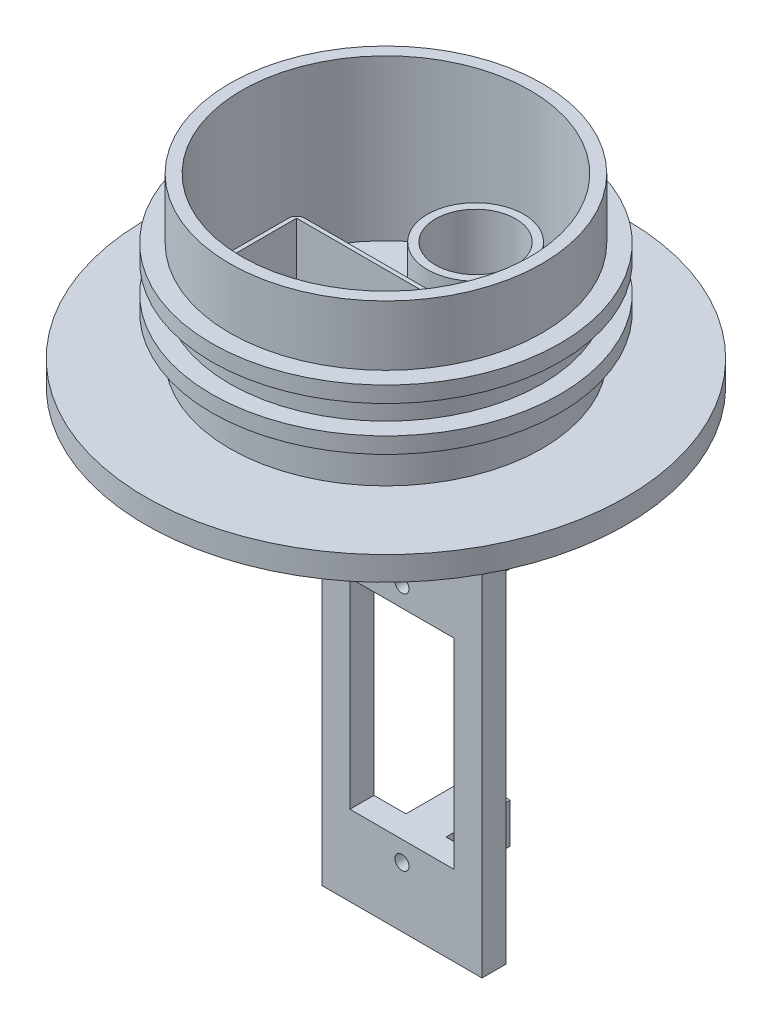
SolidWorks part; units mm, degrees
ref_plane "前基準面" through (0, 0, 0) normal (0, 0, 1) x (1, 0, 0)
ref_plane "上基準面" through (0, 0, 0) normal (0, 1, 0) x (1, 0, 0)
ref_plane "右基準面" through (0, 0, 0) normal (1, 0, 0) x (0, 0, -1)
sketch "草圖1" plane through (0, 0, 0) normal (0, 1, 0) x (1, 0, 0)
  circle A0 centre (0, 0) radius 19.5
  circle A1 centre (0, 0) radius 18
  dimension "D1" = 39
  dimension "D2" = 36
extrude "填料-伸長1" add sketch "草圖1" along normal blind 20
sketch "草圖3" plane through (0, 0, 0) normal (0, -1, 0) x (1, 0, 0)
  circle A0 centre (0, 0) radius 30
  dimension "D1" = 60
extrude "填料-伸長2" add sketch "草圖3" along normal blind 3
sketch "草圖4" plane through (0, 0, 0) normal (0, 0, 1) x (1, 0, 0)
  line L0 (0, 20) -> (0, -52.6673) construction
  line L1 (18, 20) -> (-18, 20) construction
  line L2 (-30, -3) -> (30, -3) construction
  line L3 (-10, -3) -> (10, -3)
  line L4 (-10, -3) -> (-10, -63)
  line L5 (-10, -63) -> (10, -63)
  line L6 (10, -3) -> (10, -63)
  line L8 (-6.5, -28) -> (6.5, -28)
  line L9 (-6.5, -28) -> (-6.5, -53)
  line L10 (-6.5, -53) -> (6.5, -53)
  line L11 (6.5, -28) -> (6.5, -53)
  dimension "D1" = 10
  dimension "D2" = 10
  dimension "D3" = 60
  dimension "D4" = 6.5
  dimension "D5" = 6.5
  dimension "D6" = 25
  dimension "D7" = 25
ref_plane "平面2" through (0, -3, 0) normal (0, -1, 0) x (-1, 0, 0)
sketch "草圖10" plane through (0, -3, 0) normal (0, -1, 0) x (-1, 0, 0)
  circle A0 centre (0, 11.196) radius 5
  circle A1 centre (0, 11.196) radius 6
  dimension "D1" = 10
  dimension "D2" = 12
extrude "填料-伸長6" add sketch "草圖10" against normal blind 10
sketch "草圖11" plane through (0, -3, 0) normal (0, -1, 0) x (-1, 0, 0)
  circle A0 centre (0, 11.196) radius 5.0075
extrude "除料-伸長4" cut sketch "草圖11" along normal blind 19 and the other way blind 10
sketch "草圖12" plane through (0, -3, 0) normal (0, -1, 0) x (1, 0, 0)
  line L0 (0, 18) -> (0, -18) construction
  line L2 (-10.75, 13.408) -> (10.75, 13.408)
  line L3 (-10.75, 13.408) -> (-10.75, 0.408)
  line L4 (-10.75, 0.408) -> (10.75, 0.408)
  line L5 (10.75, 13.408) -> (10.75, 0.408)
  circle A0 centre (0, 0) radius 18 construction
  dimension "D1" = 21.5
  dimension "D2" = 13
  dimension "D3" = 10.75
ref_plane "平面4" through (0, 0, -3) normal (0, 0, 1) x (1, 0, 0)
sketch "草圖15" plane through (0, 0, -3) normal (0, 0, 1) x (1, 0, 0)
  line L0 (0, 20) -> (0, -63) construction
  line L1 (-10, -3) -> (10, -3)
  line L2 (-10, -3) -> (-10, -63)
  line L3 (-10, -63) -> (10, -63)
  line L4 (10, -3) -> (10, -63)
  line L5 (-6.5, -28) -> (6.5, -28)
  line L6 (-6.5, -28) -> (-6.5, -53)
  line L7 (-6.5, -53) -> (6.5, -53)
  line L8 (6.5, -28) -> (6.5, -53)
  dimension "D1" = 60
  dimension "D2" = 25
  dimension "D3" = 13
extrude "填料-伸長7" add sketch "草圖15" along normal blind 1 and the other way blind 2
sketch "草圖16" plane through (0, 0, -3) normal (0, 0, 1) x (1, 0, 0)
  line L0 (-6.5, -28) -> (6.5, -28) construction
  line L1 (-2.5, -28) -> (2.5, -28)
  line L2 (-2.5, -28) -> (-2.5, -23)
  line L3 (-2.5, -23) -> (2.5, -23)
  line L4 (2.5, -28) -> (2.5, -23)
  line L5 (-6.5, -53) -> (6.5, -53) construction
  line L6 (-2.5, -53) -> (2.5, -53)
  line L7 (-2.5, -53) -> (-2.5, -58)
  line L8 (-2.5, -58) -> (2.5, -58)
  line L9 (2.5, -53) -> (2.5, -58)
  line L10 (0, 20) -> (0, -52.6673) construction
  dimension "D1" = 5
  dimension "D2" = 5
  dimension "D3" = 2.5
  dimension "D4" = 5
  dimension "D5" = 5
  dimension "D6" = 2.5
extrude "填料-伸長8" add sketch "草圖16" against normal blind 10
sketch "草圖18" plane through (0, 0, 0) normal (0, 0, 1) x (1, 0, 0)
  line L0 (-2.5, -25.5) -> (2.5, -25.5) construction
  line L1 (-2.5, -28) -> (-2.5, -23) construction
  line L2 (2.5, -28) -> (2.5, -23) construction
  line L3 (-2.5, -55.5) -> (2.5, -55.5) construction
  line L4 (-2.5, -53) -> (-2.5, -58) construction
  line L5 (2.5, -53) -> (2.5, -58) construction
  circle A0 centre (0, -55.5) radius 0.875
  circle A1 centre (0, -25.5) radius 0.875
  dimension "D1" = 1.75
  dimension "D2" = 1.75
extrude "除料-伸長5" cut sketch "草圖18" against normal blind 39 and the other way blind 10
extrude "除料-伸長6" cut sketch "草圖12" against normal blind 21.5 contours L5 L4 L3 L2
ref_plane "平面5" through (0, 0, 0) normal (0, 1, 0) x (1, 0, 0)
sketch "草圖19" plane through (0, 0, 0) normal (0, 1, 0) x (1, 0, 0)
  line L0 (-10.75, -13.408) -> (10.75, -13.408) construction
  line L1 (-11.25, 0.092) -> (11.25, 0.092)
  line L2 (-11.25, 0.092) -> (-11.25, -13.908)
  line L3 (-11.25, -13.908) -> (11.25, -13.908)
  line L4 (11.25, 0.092) -> (11.25, -13.908)
  line L5 (-10.75, -13.408) -> (-10.75, -0.408) construction
  line L6 (10.75, -13.408) -> (10.75, -0.408) construction
  line L8 (-10.75, -0.408) -> (10.75, -0.408) construction
  line L10 (-10.75, -0.408) -> (10.75, -0.408)
  line L11 (-10.75, -0.408) -> (-10.75, -13.408)
  line L12 (-10.75, -13.408) -> (10.75, -13.408)
  line L13 (10.75, -0.408) -> (10.75, -13.408)
  dimension "D1" = 0.5
  dimension "D2" = 0.5
  dimension "D3" = 0.5
  dimension "D4" = 0.5
extrude "填料-伸長9" add sketch "草圖19" along normal blind 10
fillet "圓角2" radius 1 1 edges at (-11.25, 5, -0.092)
fillet "圓角3" radius 1 1 edges at (11.25, 5, -0.092)
fillet "圓角4" radius 1 1 edges at (11.25, 5, 13.908)
fillet "圓角5" radius 1 1 edges at (-11.25, 5, 13.908)
ref_plane "平面6" through (0, 7, 0) normal (0, -1, 0) x (-1, 0, 0)
sketch "草圖25" plane through (0, 7, 0) normal (0, -1, 0) x (-1, 0, 0)
  circle A0 centre (0, 0) radius 21.75
  circle A1 centre (0, 0) radius 19.5
  dimension "D1" = 43.5
extrude "填料-伸長12" add sketch "草圖25" along normal blind 2
ref_plane "平面10" through (0, 10.5, 0) normal (0, -1, 0) x (-1, 0, 0)
sketch "草圖26" plane through (0, 10.5, 0) normal (0, -1, 0) x (-1, 0, 0)
  circle A0 centre (0, 0) radius 21.75
  circle A1 centre (0, 0) radius 19.5
extrude "填料-伸長13" add sketch "草圖26" against normal blind 2
